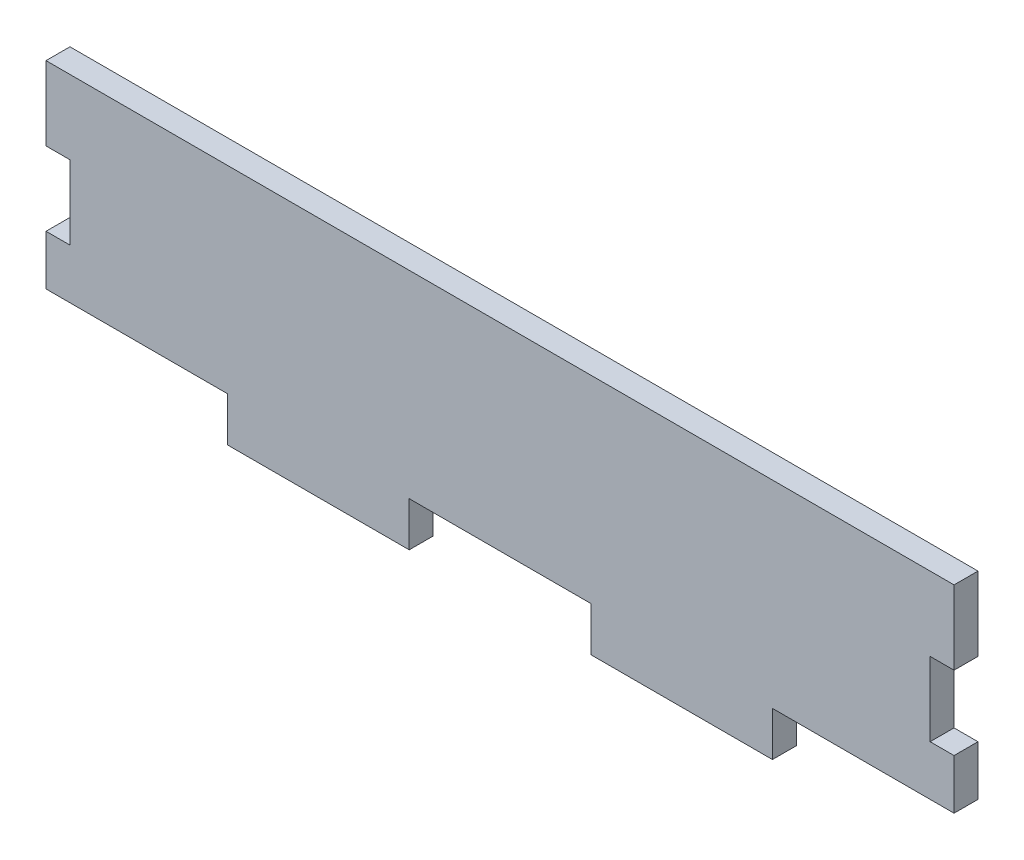
SolidWorks part; units mm, degrees
ref_plane "Ön Düzlem" through (0, 0, 0) normal (0, 0, 1) x (1, 0, 0)
ref_plane "Üst Düzlem" through (0, 0, 0) normal (0, 1, 0) x (1, 0, 0)
ref_plane "Sağ Düzlem" through (0, 0, 0) normal (1, 0, 0) x (0, 0, -1)
sketch "Sketch1" plane through (0, 0, 0) normal (0, 0, 1) x (1, 0, 0)
  line L4 (-51.2, -9.8) -> (-51.2, -4.1667)
  line L5 (-51.2, 12.5) -> (51.2, 12.5)
  line L6 (51.2, -4.1667) -> (51.2, -9.8)
  line L7 (-51.2, 4.1667) -> (-51.2, 12.5)
  line L8 (51.2, 4.1667) -> (51.2, 12.5)
  line L9 (-30.72, -12.5) -> (-30.72, -9.8)
  line L10 (-51.2, -4.1667) -> (-48.5, -4.1667)
  line L11 (-51.2, 4.1667) -> (-48.5, 4.1667)
  line L16 (-10.24, -12.5) -> (-10.24, -9.8)
  line L17 (-48.5, 4.1667) -> (-48.5, -4.1667)
  line L18 (51.2, -9.8) -> (30.72, -9.8)
  line L19 (10.24, -12.5) -> (10.24, -9.8)
  line L20 (48.5, 4.1667) -> (48.5, -4.1667)
  line L21 (51.2, 4.1667) -> (48.5, 4.1667)
  line L22 (51.2, -4.1667) -> (48.5, -4.1667)
  line L25 (30.72, -12.5) -> (30.72, -9.8)
  line L26 (-30.72, -9.8) -> (-51.2, -9.8)
  line L27 (10.24, -9.8) -> (-10.24, -9.8)
  line L28 (-30.72, -12.5) -> (-30.72, -14.8)
  line L29 (-30.72, -14.8) -> (-10.24, -14.8)
  line L30 (30.72, -14.8) -> (30.72, -12.5)
  line L31 (10.24, -12.5) -> (10.24, -14.8)
  line L32 (-10.24, -12.5) -> (-10.24, -14.8)
  line L33 (10.24, -14.8) -> (30.72, -14.8)
  point P0 (0, 0)
extrude "Boss-Extrude1" add sketch "Sketch1" along normal blind 2.7
